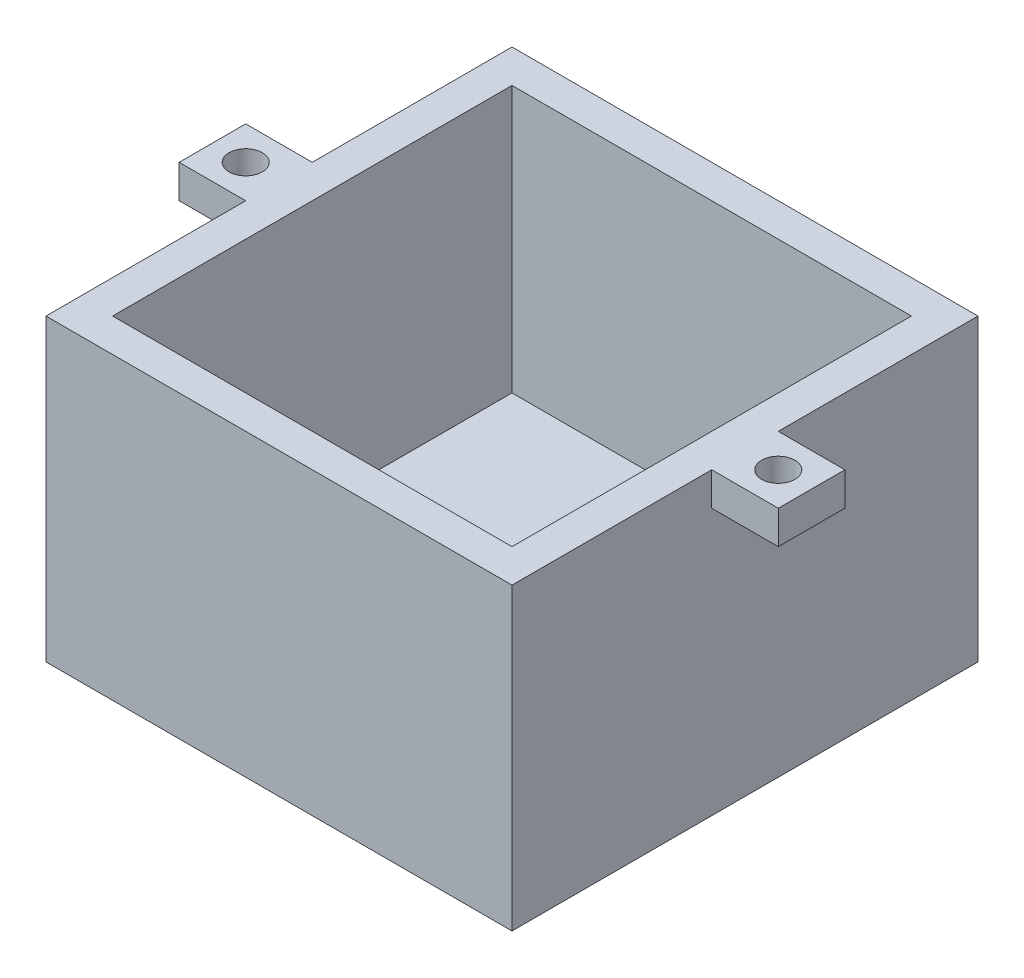
SolidWorks part; units mm, degrees
ref_plane "Front" through (0, 0, 0) normal (0, 0, 1) x (1, 0, 0)
ref_plane "Top" through (0, 0, 0) normal (0, 1, 0) x (1, 0, 0)
ref_plane "Right" through (0, 0, 0) normal (1, 0, 0) x (0, 0, -1)
sketch "Sketch1" plane through (0, 0, 0) normal (0, 1, 0) x (1, 0, 0)
  line L1 (0, 0) -> (76.2, 0)
  line L2 (0, 0) -> (0, 76.2)
  line L3 (0, 76.2) -> (76.2, 76.2)
  line L4 (76.2, 0) -> (76.2, 76.2)
  line L5 (-6.35, -6.35) -> (82.55, -6.35)
  line L6 (-6.35, -6.35) -> (-6.35, 82.55)
  line L7 (-6.35, 82.55) -> (82.55, 82.55)
  line L8 (82.55, -6.35) -> (82.55, 82.55)
  dimension "D1" = 76.2
  dimension "D2" = 76.2
  dimension "D3" = 88.9
  dimension "D4" = 6.35
  dimension "D5" = 6.35
  dimension "D6" = 6.35
extrude "Boss-Extrude1" add sketch "Sketch1" along normal blind 50.8
sketch "Sketch2" plane through (0, 0, 0) normal (0, -1, 0) x (1, 0, 0)
  line L1 (-6.35, -82.55) -> (82.55, -82.55)
  line L2 (-6.35, -82.55) -> (-6.35, 6.35)
  line L3 (-6.35, 6.35) -> (82.55, 6.35)
  line L4 (82.55, -82.55) -> (82.55, 6.35)
extrude "Boss-Extrude2" add sketch "Sketch2" along normal blind 6.35
sketch "Sketch3" plane through (0, 50.8, 0) normal (0, 1, 0) x (1, 0, 0)
  line L0 (82.55, -6.35) -> (82.55, 82.55) construction
  line L1 (82.55, 44.45) -> (95.25, 44.45)
  line L2 (82.55, 44.45) -> (82.55, 31.75)
  line L3 (82.55, 31.75) -> (95.25, 31.75)
  line L4 (95.25, 44.45) -> (95.25, 31.75)
  line L5 (38.1, 76.2) -> (38.1, 0) construction
  line L6 (76.2, 76.2) -> (0, 76.2) construction
  line L7 (0, 0) -> (76.2, 0) construction
  line L8 (-19.05, 44.45) -> (-19.05, 31.75)
  line L9 (-6.35, 31.75) -> (-19.05, 31.75)
  line L10 (-6.35, 44.45) -> (-6.35, 31.75)
  line L11 (-6.35, 44.45) -> (-19.05, 44.45)
  point P6 (82.55, 38.1)
  point P7 (95.25, 38.1)
  dimension "D1" = 12.7
  dimension "D2" = 12.7
extrude "Boss-Extrude3" add sketch "Sketch3" against normal blind 6.35
sketch "Sketch4" plane through (0, 50.8, 0) normal (0, 1, 0) x (1, 0, 0)
  line L0 (38.1, 76.2) -> (38.1, 0) construction
  line L1 (76.2, 76.2) -> (0, 76.2) construction
  line L2 (0, 0) -> (76.2, 0) construction
  line L3 (95.25, 31.75) -> (95.25, 44.45) construction
  circle A0 centre (88.9, 38.1) radius 3.175
  circle A1 centre (-12.7, 38.1) radius 3.175
  point P12 (95.25, 38.1)
  dimension "D1" = 6.35
extrude "Cut-Extrude1" cut sketch "Sketch4" against normal through all
